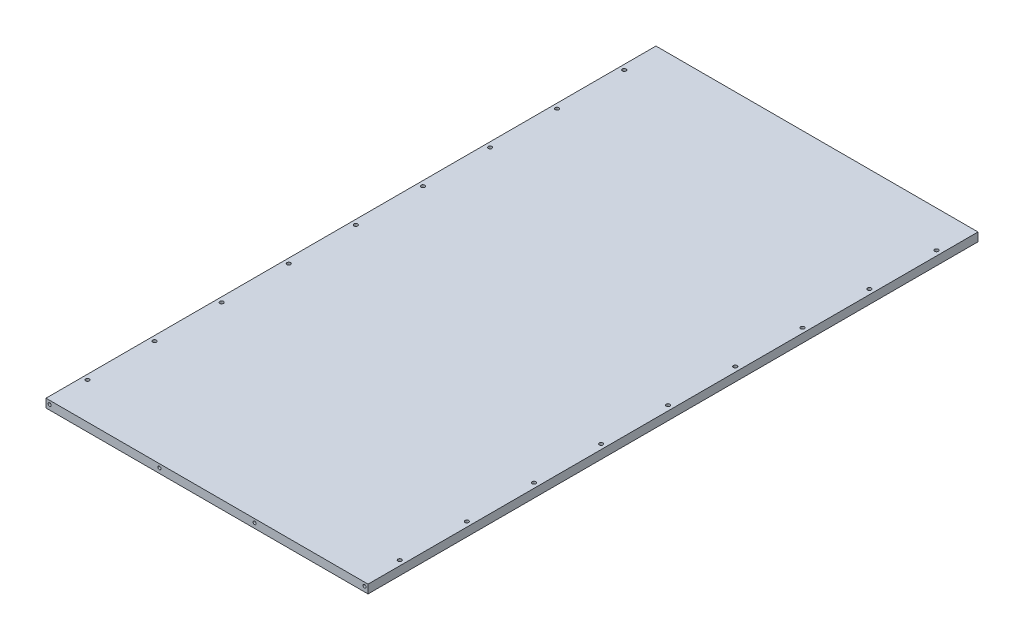
SolidWorks part; units mm, degrees
material "2014 Alloy"
ref_plane "Front Plane" through (0, 0, 0) normal (0, 0, 1) x (1, 0, 0)
ref_plane "Top Plane" through (0, 0, 0) normal (0, 1, 0) x (1, 0, 0)
ref_plane "Right Plane" through (0, 0, 0) normal (1, 0, 0) x (0, 0, -1)
sketch "Sketch1" plane through (0, 0, 0) normal (0, 1, 0) x (1, 0, 0)
  line L1 (-132, 250) -> (132, 250)
  line L2 (-132, 250) -> (-132, -250)
  line L3 (-132, -250) -> (132, -250)
  line L4 (132, 250) -> (132, -250)
  line L5 (-132, 250) -> (132, -250) construction
  line L6 (-132, -250) -> (132, 250) construction
  point P0 (0, 0)
  dimension "D1" = 264
  dimension "D2" = 500
extrude "Boss-Extrude1" add sketch "Sketch1" along normal blind 7
sketch "Sketch2" plane through (0, 0, 0) normal (0, -1, 0) x (1, 0, 0)
  line L0 (-132, 250) -> (132, 250) construction
  line L1 (122, 230) -> (122, -230) construction
  line L2 (132, 250) -> (132, -250) construction
  line L4 (112, -240) -> (-112, -240) construction
  line L5 (-122, -230) -> (-122, 230) construction
  line L6 (-112, 240) -> (112, 240) construction
  line L7 (-132, -250) -> (-132, 250) construction
  line L8 (132, -250) -> (-132, -250) construction
  line L9 (123, 230) -> (123, -230)
  line L10 (112, -241) -> (-112, -241)
  line L11 (-123, -230) -> (-123, 230)
  line L12 (-112, 241) -> (112, 241)
  line L13 (121, 230) -> (121, -230)
  line L14 (112, -239) -> (-112, -239)
  line L15 (-121, -230) -> (-121, 230)
  line L16 (-112, 239) -> (112, 239)
  arc A0 (112, 240) -> (122, 230) centre (112, 230) cw construction
  arc A1 (122, -230) -> (112, -240) centre (112, -230) cw construction
  arc A2 (-112, -240) -> (-122, -230) centre (-112, -230) cw construction
  arc A3 (-122, 230) -> (-112, 240) centre (-112, 230) cw construction
  arc A4 (123, -230) -> (112, -241) centre (112, -230) cw
  arc A5 (-112, -241) -> (-123, -230) centre (-112, -230) cw
  arc A6 (-123, 230) -> (-112, 241) centre (-112, 230) cw
  arc A7 (112, 241) -> (123, 230) centre (112, 230) cw
  arc A8 (121, -230) -> (112, -239) centre (112, -230) cw
  arc A9 (-112, -239) -> (-121, -230) centre (-112, -230) cw
  arc A10 (-121, 230) -> (-112, 239) centre (-112, 230) cw
  arc A11 (112, 239) -> (121, 230) centre (112, 230) cw
  dimension "D3" = 10
  dimension "D6" = 10
  dimension "D1" = 10
  dimension "D2" = 10
  dimension "D4" = 10
  dimension "D5" = 10
  dimension "D7" = 1
  dimension "D8" = 1
extrude "Cut-Extrude1" cut sketch "Sketch2" against normal blind 1
hole_wizard "Ø3.0mm Dowel Hole1" positions "Sketch4" profile "Sketch3" hole size "Ø3.0" standard "ISO"
sketch "Sketch4" plane through (0, 7, 0) normal (0, 1, 0) x (1, 0, 0)
  line L0 (-132, -250) -> (132, -250) construction
  line L1 (132, -250) -> (132, 250) construction
  line L2 (132, 0) -> (-132, 0) construction
  line L3 (-132, 250) -> (-132, -250) construction
  point P0 (128, -220)
  point P2 (128, -165)
  point P6 (128, -110)
  point P8 (128, -55)
  point P23 (128, 0)
  dimension "D1" = 30
  dimension "D2" = 55
  dimension "D3" = 55
  dimension "D4" = 55
  dimension "D5" = 4
sketch "Sketch3" plane through (128, 7, 220) normal (1, 0, 0) x (0, 0, 1)
  line L0 (0, 0) -> (0, 15.9013)
  line L1 (0, 15.9013) -> (1.5, 15)
  line L2 (1.5, 15) -> (1.5, 0)
  line L5 (1.5, 0) -> (0, 0)
  line L10 (0, 15.9013) -> (-1.5, 15) construction
  line L11 (0, -6.35) -> (0, 107.95) construction
  dimension "Hole Dia." = 3
  dimension "Hole Depth" = 15
  dimension "Drill Angle" = 118
mirror "Mirror1" about plane through (0, 0, 0) normal (0, 0, 1) of "Ø3.0mm Dowel Hole1"
mirror "Mirror2" about plane through (0, 0, 0) normal (1, 0, 0) of "Mirror1", "Ø3.0mm Dowel Hole1"
sketch "Sketch5" plane through (0, 0, 0) normal (0, -1, 0) x (-1, 0, 0)
  line L0 (112, -230) -> (-112, -230)
  line L1 (-112, -230) -> (112, -10)
  line L2 (112, -10) -> (112, -230)
  line L3 (132, -250) -> (-132, -250) construction
  line L4 (132, 250) -> (132, -250) construction
  line L5 (-132, -250) -> (-132, 250) construction
  line L6 (97.7287, -10) -> (-112, -215.9836)
  line L7 (-112, -215.9836) -> (-112, -10)
  line L8 (-112, -10) -> (97.7287, -10)
  line L9 (132, 0) -> (-132, 0) construction
  line L10 (-112, 10) -> (97.7287, 10)
  line L11 (-112, 215.9836) -> (-112, 10)
  line L12 (97.7287, 10) -> (-112, 215.9836)
  line L13 (112, 10) -> (112, 230)
  line L14 (-112, 230) -> (112, 10)
  line L15 (112, 230) -> (-112, 230)
  dimension "D1" = 20
  dimension "D2" = 20
  dimension "D3" = 20
  dimension "D4" = 20
  dimension "D5" = 10
  dimension "D6" = 10
  dimension "D7" = 10
extrude "Cut-Extrude2" cut sketch "Sketch5" against normal blind 6
fillet "Fillet1" radius 4 12 edges at (-112, 3, -230) (-112, 3, -10) (112, 3, -230) (112, 3, -215.9836) (112, 3, -10) (-97.7287, 3, -10) (112, 3, 10) (-97.7287, 3, 10) (-112, 3, 10) (-112, 3, 230) (112, 3, 230) (112, 3, 215.9836)
hole_wizard "M3 Tapped Hole2" positions "Sketch7" profile "Sketch6" tap size "M3" standard "ISO"
sketch "Sketch7" plane through (0, 0, 250) normal (0, 0, 1) x (1, 0, 0)
  line L0 (-132, 7) -> (-132, 0) construction
  line L1 (132, 7) -> (132, 0) construction
  line L3 (-132, 7) -> (132, 7) construction
  point P0 (-129, 4)
  point P2 (-39, 4)
  point P4 (39, 4)
  point P6 (129, 4)
  dimension "D1" = 3
  dimension "D2" = 3
  dimension "D3" = 90
  dimension "D4" = 90
  dimension "D5" = 3
sketch "Sketch6" plane through (-129, 4, 250) normal (1, 0, 0) x (0, -1, 0)
  line L0 (0, 0) -> (0, 8.2511)
  line L1 (0, 8.2511) -> (1.25, 7.5)
  line L2 (1.25, 7.5) -> (1.25, 0)
  line L5 (1.25, 0) -> (0, 0)
  line L10 (0, 8.2511) -> (-1.25, 7.5) construction
  line L11 (0, -6.35) -> (0, 107.95) construction
  dimension "Tap Drill Dia." = 2.5
  dimension "Tap Drill Depth" = 7.5
  dimension "Drill Angle" = 118
cosmetic thread "Hole Thread5"
cosmetic thread "Hole Thread6"
cosmetic thread "Hole Thread7"
cosmetic thread "Hole Thread8"
